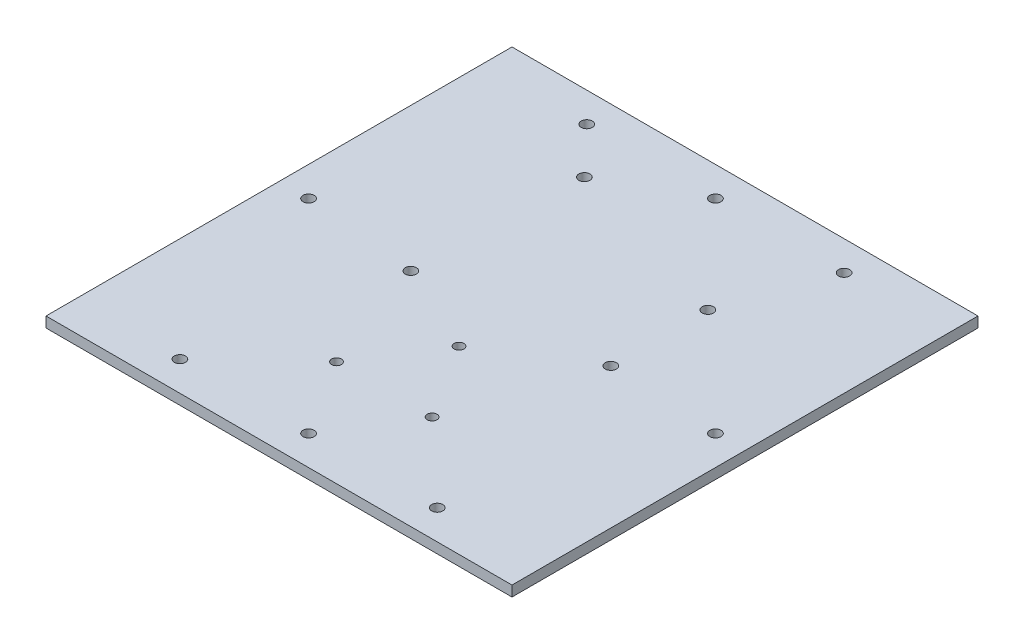
SolidWorks part; units mm, degrees
ref_plane "Front Plane" through (0, 0, 0) normal (0, 0, 1) x (1, 0, 0)
ref_plane "Top Plane" through (0, 0, 0) normal (0, 1, 0) x (1, 0, 0)
ref_plane "Right Plane" through (0, 0, 0) normal (1, 0, 0) x (0, 0, -1)
sketch "Sketch2" plane through (0, 0, 0) normal (0, 1, 0) x (1, 0, 0)
  line L0 (-67, 67) -> (67, -67) construction
  line L1 (-67, 67) -> (67, 67)
  line L2 (-67, 67) -> (-67, -67)
  line L3 (-67, -67) -> (67, -67)
  line L4 (67, 67) -> (67, -67)
  line L5 (67, 67) -> (-67, -67) construction
  line L6 (-0.0804, -25.9435) -> (-0.0804, -44.0256) construction
  line L7 (-50, 50) -> (50, -50) construction
  line L8 (50, 50) -> (-50, 50)
  line L9 (50, 50) -> (50, -50)
  line L10 (50, -50) -> (-50, -50)
  line L11 (-50, 50) -> (-50, -50)
  line L12 (50, 50) -> (-50, -50) construction
  line L13 (-25.7654, -3.3155) -> (-25.7654, 44.9845) construction
  line L14 (26.6346, 1.7845) -> (14.9379, 1.7845)
  line L15 (-25.7654, -3.3155) -> (14.9379, -3.3155)
  line L16 (14.9379, -3.3155) -> (14.9379, 1.7845)
  line L17 (0, 67) -> (0, -67) construction
  line L18 (-67, 0) -> (67, 0) construction
  line L19 (0, 67) -> (0, 50) construction
  line L20 (-50, 0) -> (-67, 0) construction
  line L21 (0, -50) -> (0, -67) construction
  line L22 (50, 0) -> (67, 0) construction
  line L23 (-37, 67) -> (-37, -67) construction
  line L24 (37, 67) -> (37, -67) construction
  line L25 (-37, 50) -> (-37, 67) construction
  line L26 (37, 50) -> (37, 67) construction
  line L27 (-37, -50) -> (-37, -67) construction
  line L28 (37, -50) -> (37, -67) construction
  circle A0 centre (-0.0804, -15.1435) radius 1.4
  circle A1 centre (-13.8304, -36.6435) radius 1.4
  circle A2 centre (13.6696, -36.6435) radius 1.4
  circle A3 centre (-24.1654, 44.9845) radius 1.6
  circle A4 centre (-25.7654, -3.3155) radius 1.6
  circle A5 centre (26.6346, 29.6845) radius 1.6
  circle A6 centre (26.6346, 1.7845) radius 1.6
  circle A10 centre (0, 58.5) radius 1.6
  circle A11 centre (-58.5, 0) radius 1.6
  circle A12 centre (0, -58.5) radius 1.6
  circle A13 centre (58.5, 0) radius 1.6
  circle A14 centre (-37, 58.5) radius 1.6
  circle A15 centre (37, 58.5) radius 1.6
  circle A16 centre (-37, -58.5) radius 1.6
  circle A17 centre (37, -58.5) radius 1.6
  point P12 (0, 0)
  point P18 (0, 0)
  point P40 (0, 58.5)
  point P44 (-58.5, 0)
  point P49 (0, -58.5)
  point P54 (58.5, 0)
  point P63 (-37, 58.5)
  point P68 (37, 58.5)
  point P73 (-37, -58.5)
  point P78 (37, -58.5)
  dimension "D3" = 30
  dimension "2.8" = 2.8
  dimension "D9" = 3.2
  dimension "D1" = 134
  dimension "D2" = 100
  dimension "D4" = 50.8
  dimension "D5" = 27.9
  dimension "D6" = 5.1
  dimension "D7" = 48.3
  dimension "D8" = 40.7033
  dimension "D10" = 30
extrude "Boss-Extrude2" add sketch "Sketch2" along normal blind 3
